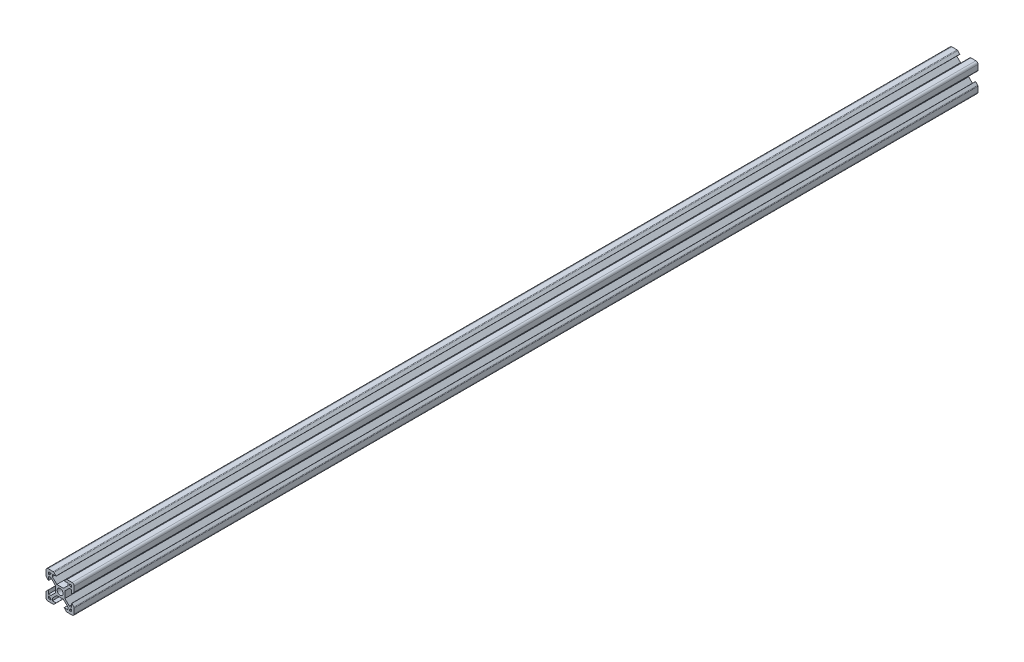
SolidWorks part; units mm, degrees
ref_plane "Front Plane" through (0, 0, 0) normal (0, 0, 1) x (1, 0, 0)
ref_plane "Top Plane" through (0, 0, 0) normal (0, 1, 0) x (1, 0, 0)
ref_plane "Right Plane" through (0, 0, 0) normal (1, 0, 0) x (0, 0, -1)
sketch "Sketch2" plane through (0, 0, 0) normal (0, 0, 1) x (1, 0, 0)
  line L0 (-8.2, 2.89) -> (-8.2, 5.5)
  line L1 (-2.1, 0) -> (-10, 0) construction
  line L2 (0, 2.1) -> (0, 10) construction
  line L3 (-4.9072, 10) -> (-8.5, 10)
  line L4 (-10, 4.9072) -> (-10, 8.5)
  line L5 (-2.1, 0) -> (-3.4, 0) construction
  line L6 (0, 2.1) -> (0, 3.4) construction
  line L7 (0, 3.4) -> (-2.3393, 3.4)
  line L8 (-3.4, 0) -> (-3.4, 2.3393)
  line L9 (-2.89, 8.2) -> (-5.5, 8.2)
  line L10 (-6.57, 8.2) -> (-6.57, 7.66)
  line L11 (-8.2, 6.57) -> (-7.66, 6.57)
  line L12 (-5.5, 8.2) -> (-5.5, 6.5607)
  line L13 (-6.5607, 5.5) -> (-8.2, 5.5)
  line L14 (-8.2, 8.2) -> (-1.4849, 1.4849) construction
  line L15 (-6.5607, 5.5) -> (-3.4, 2.3393)
  line L16 (-5.5, 6.5607) -> (-2.3393, 3.4)
  line L17 (-7.66, 6.57) -> (-6.57, 7.66)
  line L18 (-8.7303, 7.6697) -> (-0.5303, -0.5303) construction
  line L19 (-7.6697, 8.7303) -> (0.5303, 0.5303) construction
  line L20 (-8.2, 8.2) -> (0, 0) construction
  line L21 (-8.2, 6.57) -> (-8.2, 8.2)
  line L22 (-8.2, 0) -> (-8.2, 8.2) construction
  line L23 (-6.57, 8.2) -> (-8.2, 8.2)
  line L24 (0, 8.2) -> (-8.2, 8.2) construction
  line L25 (-10, 0) -> (-10, 10) construction
  line L26 (0, 10) -> (-10, 10) construction
  line L27 (-2.89, 8.31) -> (-2.89, 8.2)
  line L29 (-8.31, 2.89) -> (-8.2, 2.89)
  line L30 (-4.3486, 9.7686) -> (-2.89, 8.31)
  line L31 (-8.31, 2.89) -> (-9.7686, 4.3486)
  arc A0 (0, 2.1) -> (-2.1, 0) centre (0, 0) ccw
  arc A1 (-10, 8.5) -> (-8.5, 10) centre (-8.5, 8.5) cw
  arc A2 (-9.7686, 4.3486) -> (-10, 4.9072) centre (-9.21, 4.9072) cw
  arc A3 (-4.3486, 9.7686) -> (-4.9072, 10) centre (-4.9072, 9.21) ccw
  point P29 (-10, 10)
  point P39 (-10, 4.58)
  point P42 (-4.58, 10)
  dimension "D3" = 2.1
  dimension "D15" = 1.5
  dimension "D22" = 0.79
  dimension "D1" = 10
  dimension "D2" = 10
  dimension "D4" = 1.8
  dimension "D5" = 3.43
  dimension "D6" = 3.43
  dimension "D7" = 0.54
  dimension "D8" = 0.54
  dimension "D9" = 1.07
  dimension "D10" = 1.07
  dimension "D11" = 3.4
  dimension "D12" = 3.4
  dimension "D16" = 7.11
  dimension "D17" = 0.11
  dimension "D18" = 1.69
  dimension "D19" = 0.11
  dimension "D20" = 7.11
  dimension "D21" = 1.69
  dimension "D13" = 0.75
  dimension "D14" = 0.75
sketch "Sketch6" plane through (0, 0, 0) normal (0, 0, 1) x (1, 0, 0)
  line L0 (-3.4, 0) -> (-3.4, 2.3393) construction
  line L1 (-6.5607, 5.5) -> (-3.4, 2.3393) construction
  line L2 (-6.5607, 5.5) -> (-8.2, 5.5) construction
  line L3 (-8.2, 2.89) -> (-8.2, 5.5) construction
  line L4 (-8.31, 2.89) -> (-8.2, 2.89) construction
  line L5 (-7.66, 6.57) -> (-6.57, 7.66)
  line L6 (-6.57, 7.66) -> (-6.57, 8.2)
  line L7 (-6.57, 8.2) -> (-8.2, 8.2)
  line L8 (-8.2, 8.2) -> (-8.2, 6.57)
  line L9 (-8.2, 6.57) -> (-7.66, 6.57)
  line L10 (-7.66, 6.57) -> (-6.57, 7.66)
  line L11 (-6.57, 7.66) -> (-6.57, 8.2)
  line L12 (-6.57, 8.2) -> (-8.2, 8.2)
  line L13 (-8.2, 8.2) -> (-8.2, 6.57)
  line L14 (-8.2, 6.57) -> (-7.66, 6.57)
  line L15 (-8.31, 2.89) -> (-9.7686, 4.3486) construction
  line L16 (-10, 4.9072) -> (-10, 8.5) construction
  line L17 (-4.9072, 10) -> (-8.5, 10) construction
  line L18 (-4.3486, 9.7686) -> (-2.89, 8.31) construction
  line L19 (-2.89, 8.31) -> (-2.89, 8.2) construction
  line L20 (-2.89, 8.2) -> (-5.5, 8.2) construction
  line L21 (-5.5, 8.2) -> (-5.5, 6.5607) construction
  line L22 (-5.5, 6.5607) -> (-2.3393, 3.4) construction
  line L23 (0, 3.4) -> (-2.3393, 3.4) construction
  line L24 (-3.4, -2.3393) -> (-3.4, 2.3393)
  line L25 (-6.5607, 5.5) -> (-3.4, 2.3393)
  line L26 (-6.5607, 5.5) -> (-8.2, 5.5)
  line L27 (-8.2, 2.89) -> (-8.2, 5.5)
  line L28 (-8.31, 2.89) -> (-8.2, 2.89)
  line L29 (-8.31, 2.89) -> (-9.7686, 4.3486)
  line L30 (-10, 4.9072) -> (-10, 8.5)
  line L31 (-4.9072, 10) -> (-8.5, 10)
  line L32 (-4.3486, 9.7686) -> (-2.89, 8.31)
  line L33 (-2.89, 8.31) -> (-2.89, 8.2)
  line L34 (-2.89, 8.2) -> (-5.5, 8.2)
  line L35 (-5.5, 8.2) -> (-5.5, 6.5607)
  line L36 (-5.5, 6.5607) -> (-2.3393, 3.4)
  line L37 (2.3393, 3.4) -> (-2.3393, 3.4)
  line L38 (0, 2.1) -> (0, 10) construction
  line L39 (-2.1, 0) -> (-10, 0) construction
  line L40 (0, 2.1) -> (0, 10) construction
  line L41 (-2.1, 0) -> (-10, 0) construction
  line L42 (2.1, 0) -> (10, 0) construction
  line L43 (5.5, 6.5607) -> (2.3393, 3.4)
  line L44 (5.5, 8.2) -> (5.5, 6.5607)
  line L45 (2.89, 8.2) -> (5.5, 8.2)
  line L46 (2.89, 8.31) -> (2.89, 8.2)
  line L47 (4.3486, 9.7686) -> (2.89, 8.31)
  line L48 (4.9072, 10) -> (8.5, 10)
  line L49 (10, 4.9072) -> (10, 8.5)
  line L50 (8.31, 2.89) -> (9.7686, 4.3486)
  line L51 (8.31, 2.89) -> (8.2, 2.89)
  line L52 (8.2, 2.89) -> (8.2, 5.5)
  line L53 (6.5607, 5.5) -> (8.2, 5.5)
  line L54 (6.5607, 5.5) -> (3.4, 2.3393)
  line L55 (3.4, -2.3393) -> (3.4, 2.3393)
  line L56 (8.2, 6.57) -> (7.66, 6.57)
  line L57 (8.2, 8.2) -> (8.2, 6.57)
  line L58 (6.57, 8.2) -> (8.2, 8.2)
  line L59 (6.57, 7.66) -> (6.57, 8.2)
  line L60 (7.66, 6.57) -> (6.57, 7.66)
  line L61 (0, -2.1) -> (0, -10) construction
  line L62 (7.66, -6.57) -> (6.57, -7.66)
  line L63 (6.57, -7.66) -> (6.57, -8.2)
  line L64 (6.57, -8.2) -> (8.2, -8.2)
  line L65 (8.2, -8.2) -> (8.2, -6.57)
  line L66 (8.2, -6.57) -> (7.66, -6.57)
  line L67 (6.5607, -5.5) -> (3.4, -2.3393)
  line L68 (6.5607, -5.5) -> (8.2, -5.5)
  line L69 (8.2, -2.89) -> (8.2, -5.5)
  line L70 (8.31, -2.89) -> (8.2, -2.89)
  line L71 (8.31, -2.89) -> (9.7686, -4.3486)
  line L72 (10, -4.9072) -> (10, -8.5)
  line L73 (4.9072, -10) -> (8.5, -10)
  line L74 (4.3486, -9.7686) -> (2.89, -8.31)
  line L75 (2.89, -8.31) -> (2.89, -8.2)
  line L76 (2.89, -8.2) -> (5.5, -8.2)
  line L77 (5.5, -8.2) -> (5.5, -6.5607)
  line L78 (5.5, -6.5607) -> (2.3393, -3.4)
  line L79 (2.3393, -3.4) -> (-2.3393, -3.4)
  line L80 (-5.5, -6.5607) -> (-2.3393, -3.4)
  line L81 (-5.5, -8.2) -> (-5.5, -6.5607)
  line L82 (-2.89, -8.2) -> (-5.5, -8.2)
  line L83 (-2.89, -8.31) -> (-2.89, -8.2)
  line L84 (-4.3486, -9.7686) -> (-2.89, -8.31)
  line L85 (-4.9072, -10) -> (-8.5, -10)
  line L86 (-10, -4.9072) -> (-10, -8.5)
  line L87 (-8.31, -2.89) -> (-9.7686, -4.3486)
  line L88 (-8.31, -2.89) -> (-8.2, -2.89)
  line L89 (-8.2, -2.89) -> (-8.2, -5.5)
  line L90 (-6.5607, -5.5) -> (-8.2, -5.5)
  line L91 (-6.5607, -5.5) -> (-3.4, -2.3393)
  line L92 (-8.2, -6.57) -> (-7.66, -6.57)
  line L93 (-8.2, -8.2) -> (-8.2, -6.57)
  line L94 (-6.57, -8.2) -> (-8.2, -8.2)
  line L95 (-6.57, -7.66) -> (-6.57, -8.2)
  line L96 (-7.66, -6.57) -> (-6.57, -7.66)
  arc A0 (0, 2.1) -> (-2.1, 0) centre (0, 0) ccw construction
  arc A1 (-10, 4.9072) -> (-9.7686, 4.3486) centre (-9.21, 4.9072) ccw construction
  arc A2 (-8.5, 10) -> (-10, 8.5) centre (-8.5, 8.5) ccw construction
  arc A3 (-4.3486, 9.7686) -> (-4.9072, 10) centre (-4.9072, 9.21) ccw construction
  circle A4 centre (0, 0) radius 2.1
  arc A5 (-10, 4.9072) -> (-9.7686, 4.3486) centre (-9.21, 4.9072) ccw
  arc A6 (-8.5, 10) -> (-10, 8.5) centre (-8.5, 8.5) ccw
  arc A7 (-4.3486, 9.7686) -> (-4.9072, 10) centre (-4.9072, 9.21) ccw
  arc A8 (4.3486, 9.7686) -> (4.9072, 10) centre (4.9072, 9.21) cw
  arc A9 (8.5, 10) -> (10, 8.5) centre (8.5, 8.5) cw
  arc A10 (10, 4.9072) -> (9.7686, 4.3486) centre (9.21, 4.9072) cw
  arc A11 (10, -4.9072) -> (9.7686, -4.3486) centre (9.21, -4.9072) ccw
  arc A12 (8.5, -10) -> (10, -8.5) centre (8.5, -8.5) ccw
  arc A13 (4.3486, -9.7686) -> (4.9072, -10) centre (4.9072, -9.21) ccw
  arc A14 (-4.3486, -9.7686) -> (-4.9072, -10) centre (-4.9072, -9.21) cw
  arc A15 (-8.5, -10) -> (-10, -8.5) centre (-8.5, -8.5) cw
  arc A16 (-10, -4.9072) -> (-9.7686, -4.3486) centre (-9.21, -4.9072) cw
  point P85 (3.4, 0)
  dimension "D1" = 0
extrude "Boss-Extrude1" add sketch "Sketch6" against normal blind 640
ref_plane "Middle" through (0, 0, -320) normal (0, 0, 1) x (1, 0, 0)
